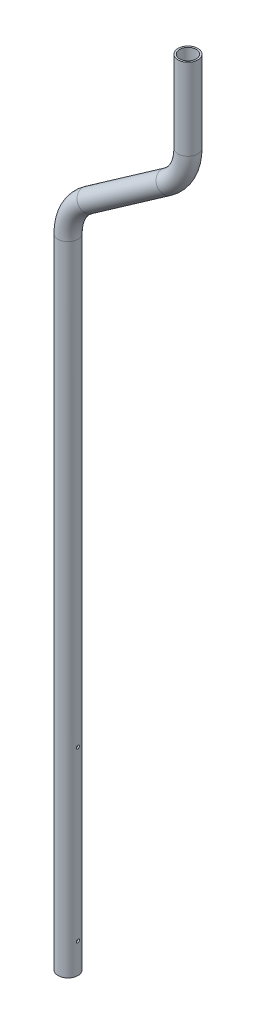
SolidWorks part; units mm, degrees
material "Plain Carbon Steel"
ref_plane "Front Plane" through (0, 0, 0) normal (0, 0, 1) x (1, 0, 0)
ref_plane "Top Plane" through (0, 0, 0) normal (0, 1, 0) x (1, 0, 0)
ref_plane "Right Plane" through (0, 0, 0) normal (1, 0, 0) x (0, 0, -1)
sketch "Sketch2" plane through (0, 0, 0) normal (0, 0, 1) x (1, 0, 0)
  line L1 (55, 0) -> (-55, 0) construction
  line L2 (0, 0) -> (0, 1350.4077)
  line L3 (0, -55) -> (0, 55) construction
  line L4 (43.3246, 1433.6335) -> (210.6754, 1550.8138)
  line L5 (254, 1634.0396) -> (254, 1806.575)
  arc A0 (210.6754, 1550.8138) -> (254, 1634.0396) centre (152.4, 1634.0396) ccw
  arc A1 (0, 1350.4077) -> (43.3246, 1433.6335) centre (101.6, 1350.4077) cw
  point P13 (254, 1581.15)
  point P16 (0, 1403.2973)
  point P19 (0, 0)
  dimension "D6" = 101.6
  dimension "D2" = 225.425
  dimension "D3" = 125
  dimension "D4" = 254
  dimension "D5" = 1806.575
ref_plane "Plane1" through (0, 1806.575, 0) normal (0, 1, 0) x (1, 0, 0)
sketch "Sketch3" plane through (0, 1806.575, 0) normal (0, 1, 0) x (1, 0, 0)
  line L0 (-55, 0) -> (55, 0) construction
  line L1 (0, -55) -> (0, 55) construction
  circle A0 centre (254, 0) radius 21.082
  circle A1 centre (254, 0) radius 17.526
  dimension "D2" = 42.164
  dimension "D3" = 35.052
  dimension "D1" = 254
sweep "Sweep1" add profiles "Sketch3" path "Sketch2"
sketch "Sketch5" plane through (0, 0, 0) normal (1, 0, 0) x (0, 0, -1)
  line L0 (-21.082, 0) -> (21.082, 0) construction
  line L2 (21.082, 0) -> (21.082, 1350.4077) construction
  circle A6 centre (0, 63.5) radius 3.3734
  circle A7 centre (0, 419.1) radius 3.3734
  point P4 (0, 0)
  dimension "D1" = 6.7469
  dimension "D4" = 21.082
  dimension "D2" = 63.5
  dimension "D3" = 355.6
extrude "Cut-Extrude1" cut sketch "Sketch5" against normal through all and the other way through all
